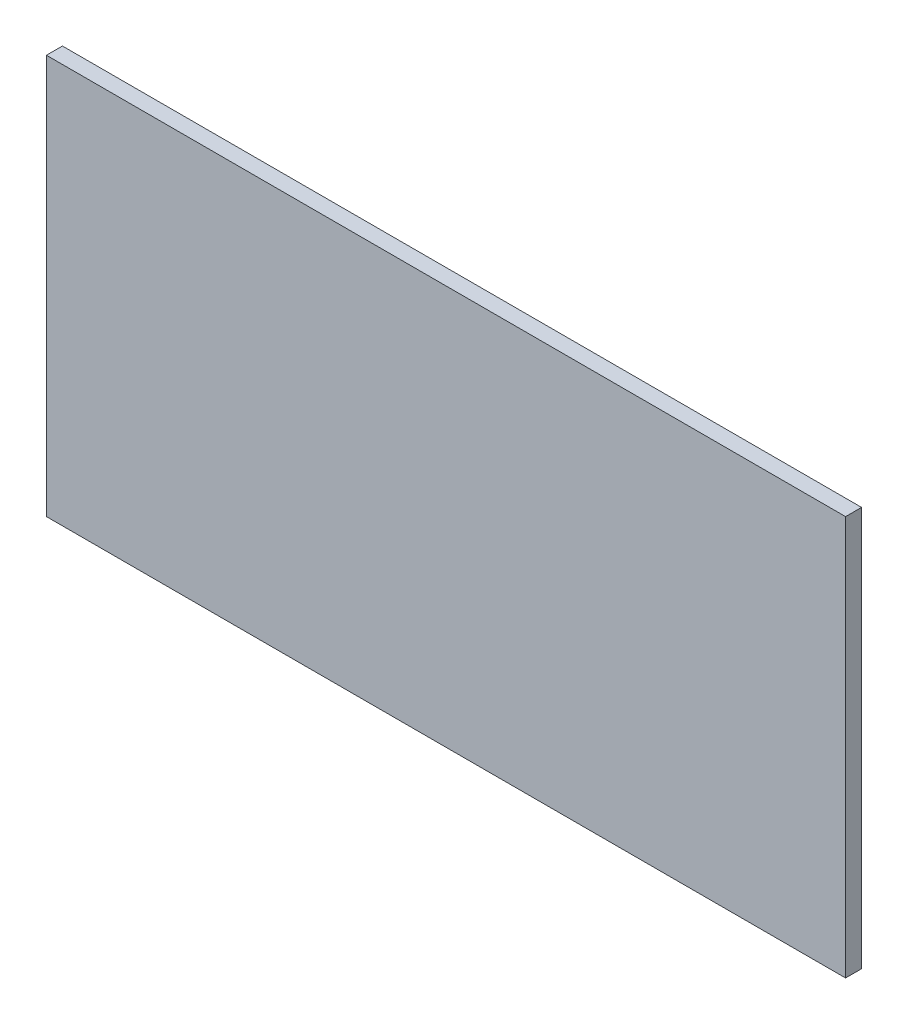
SolidWorks part; units mm, degrees
material "ABS"
ref_plane "Front Plane" through (0, 0, 0) normal (0, 0, 1) x (1, 0, 0)
ref_plane "Top Plane" through (0, 0, 0) normal (0, 1, 0) x (1, 0, 0)
ref_plane "Right Plane" through (0, 0, 0) normal (1, 0, 0) x (0, 0, -1)
sketch "Sketch1" plane through (0, 0, 0) normal (0, 0, 1) x (1, 0, 0)
  line L1 (-500, 250) -> (500, 250)
  line L2 (-500, 250) -> (-500, -250)
  line L3 (-500, -250) -> (500, -250)
  line L4 (500, 250) -> (500, -250)
extrude "Boss-Extrude1" add sketch "Sketch1" along normal blind 20
